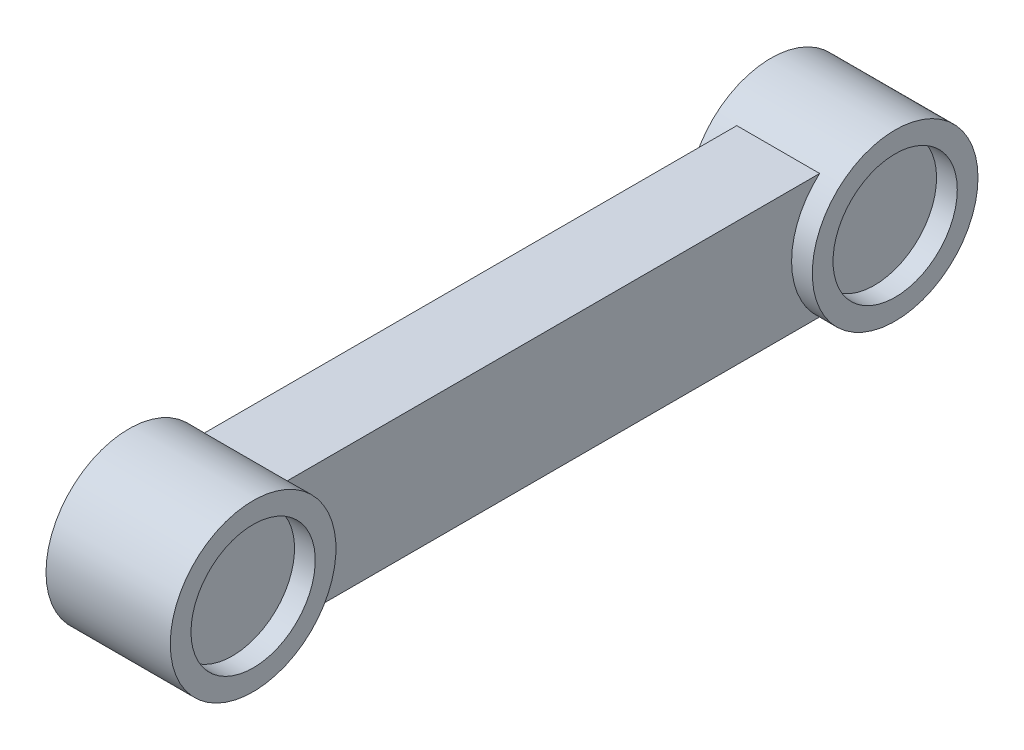
SolidWorks part; units mm, degrees
ref_plane "Front Plane" through (0, 0, 0) normal (0, 0, 1) x (1, 0, 0)
ref_plane "Top Plane" through (0, 0, 0) normal (0, 1, 0) x (1, 0, 0)
ref_plane "Right Plane" through (0, 0, 0) normal (1, 0, 0) x (0, 0, -1)
sketch "Sketch1" plane through (0, 0, 0) normal (1, 0, 0) x (0, 0, -1)
  line L0 (0, 0) -> (-309.9784, 3.6591) construction
  line L1 (-154.9892, 1.8296) -> (-154.9892, 94.4257) construction
  circle A0 centre (0, 0) radius 40
  circle A1 centre (-309.9784, 0) radius 40
  dimension "D1" = 80
  dimension "D2" = 310
extrude "Boss-Extrude1" add sketch "Sketch1" along normal blind 60
sketch "Sketch2" plane through (60, 0, 0) normal (1, 0, 0) x (0, 0, -1)
  line L0 (0, 0) -> (-309.9784, 0) construction
  line L1 (-154.9892, 0) -> (-154.9892, 81.8186) construction
  circle A0 centre (0, 0) radius 30
  circle A1 centre (-309.9784, 0) radius 30
  dimension "D1" = 60
sketch3d "3DSketch3"
  point P0 (27.7693, 11.4724, -38.3195)
ref_plane "Plane5" through (0, 0, 161.6805) normal (0, 0, -1) x (-1, 0, 0)
sketch "Sketch5" plane through (0, 0, 161.6805) normal (0, 0, -1) x (-1, 0, 0)
  line L0 (0, 0) -> (-30, 0) construction
  line L2 (-50, 30) -> (-10, 30)
  line L3 (-50, 30) -> (-50, -30)
  line L4 (-50, -30) -> (-10, -30)
  line L5 (-10, 30) -> (-10, -30)
  line L6 (-50, 30) -> (-10, -30) construction
  line L7 (-50, -30) -> (-10, 30) construction
  dimension "D1" = 30
  dimension "D2" = 40
  dimension "D3" = 60
extrude "Boss-Extrude2" add sketch "Sketch5" along normal up to surface and the other way up to surface
sketch "Sketch7" plane through (0, 0, 0) normal (-1, 0, 0) x (0, 0, 1)
  circle A0 centre (0, 0) radius 6
  dimension "D1" = 12
sketch "Sketch8" plane through (0, 0, 0) normal (-1, 0, 0) x (0, 0, 1)
  circle A0 centre (309.9784, 0) radius 6
  dimension "D1" = 12
extrude "Cut-Extrude5" cut sketch "Sketch7" against normal blind 10
extrude "Boss-Extrude3" add sketch "Sketch8" along normal blind 10
extrude "Cut-Extrude6" cut sketch "Sketch2" against normal blind 10
